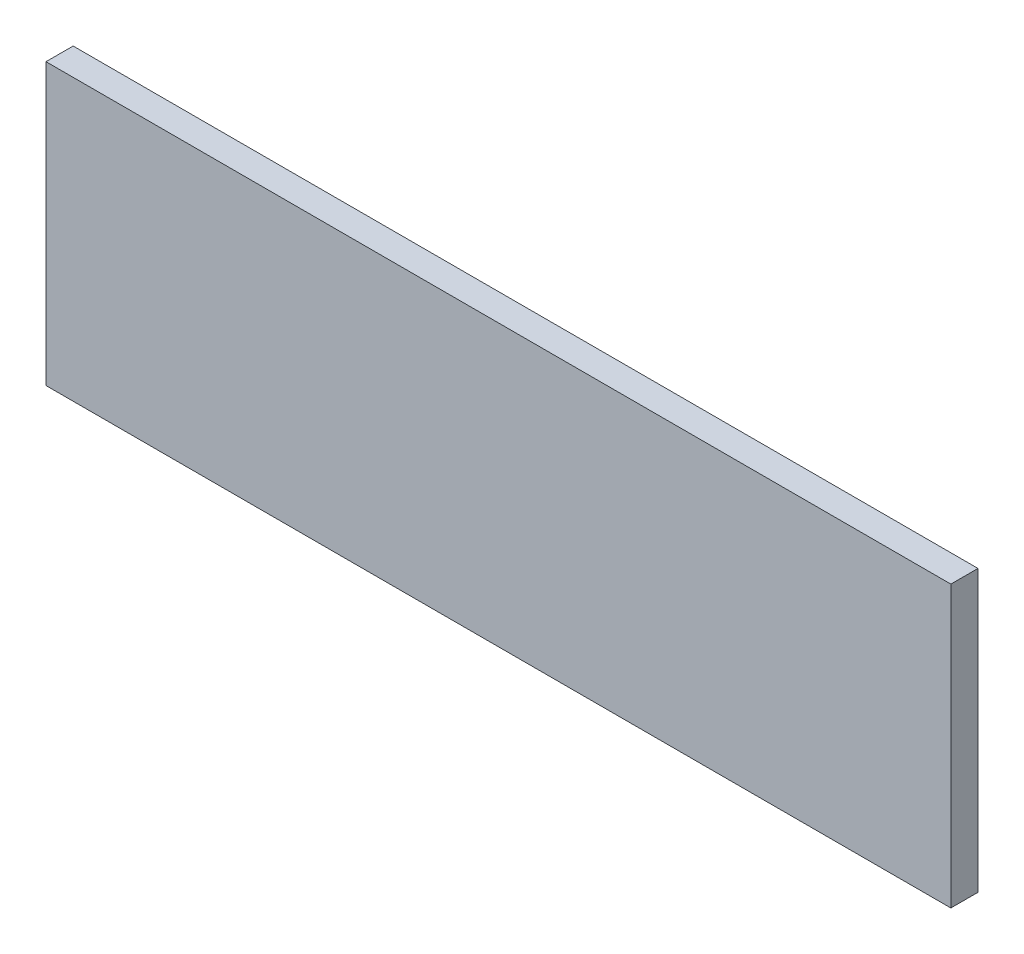
SolidWorks part; units mm, degrees
ref_plane "Plan de face" through (0, 0, 0) normal (0, 0, 1) x (1, 0, 0)
ref_plane "Plan de dessus" through (0, 0, 0) normal (0, 1, 0) x (1, 0, 0)
ref_plane "Plan de droite" through (0, 0, 0) normal (1, 0, 0) x (0, 0, -1)
sketch "Esquisse1" plane through (0, 0, 0) normal (0, 0, 1) x (1, 0, 0)
  line L1 (-50, 15.5) -> (50, 15.5)
  line L2 (-50, 15.5) -> (-50, -15.5)
  line L3 (-50, -15.5) -> (50, -15.5)
  line L4 (50, 15.5) -> (50, -15.5)
  line L5 (-50, 15.5) -> (50, -15.5) construction
  line L6 (-50, -15.5) -> (50, 15.5) construction
  point P0 (0, 0)
  dimension "D1" = 100
  dimension "D2" = 31
extrude "Boss.-Extru.1" add sketch "Esquisse1" along normal blind 3
